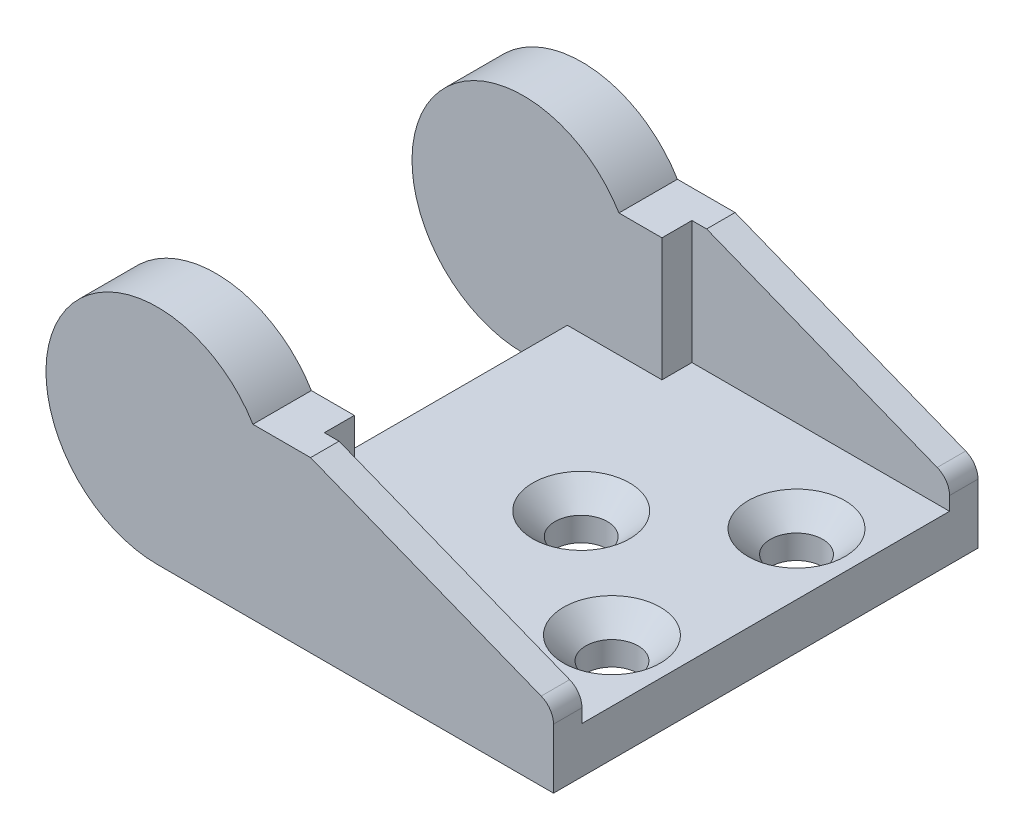
SolidWorks part; units mm, degrees
ref_plane "Front Plane" through (0, 0, 0) normal (0, 0, 1) x (1, 0, 0)
ref_plane "Top Plane" through (0, 0, 0) normal (0, 1, 0) x (1, 0, 0)
ref_plane "Right Plane" through (0, 0, 0) normal (1, 0, 0) x (0, 0, -1)
sketch "Sketch1" plane through (0, 0, 0) normal (0, 0, 1) x (1, 0, 0)
  line L0 (0, -7.25) -> (25.75, -7.25)
  line L1 (25.75, -7.25) -> (25.75, -2.5)
  line L2 (25.75, -2.5) -> (9.9548, 3.75)
  line L3 (9.9548, 3.75) -> (6.2048, 3.75)
  arc A0 (6.2048, 3.75) -> (0, -7.25) centre (0, 0) ccw
  dimension "D1" = 14.5
  dimension "D2" = 33
  dimension "D3" = 11
  dimension "D4" = 3.75
  dimension "D5" = 4.75
extrude "Boss-Extrude1" add sketch "Sketch1" along normal mid plane 27.6
sketch "Sketch2" plane through (0, 0, 0) normal (0, 1, 0) x (1, 0, 0)
  line L0 (25.75, -13.8) -> (25.75, 13.8) construction
  line L1 (25.75, 11.95) -> (9, 11.95)
  line L2 (25.75, 11.95) -> (25.75, -11.95)
  line L3 (25.75, -11.95) -> (9, -11.95)
  line L4 (9, 11.95) -> (9, -11.95)
  line L5 (25.75, 0) -> (0, 0) construction
  dimension "D1" = 23.9
  dimension "D2" = 16.75
extrude "Cut-Extrude1" cut sketch "Sketch2" against normal offset from surface 3 and the other way through all up to face at (12.875, -7.25, 0)
sketch "Sketch3" plane through (0, -7.25, 0) normal (0, -1, 0) x (1, 0, 0)
  line L0 (-7.25, 13.8) -> (-7.25, -13.8) construction
  line L1 (2.85, -10) -> (-7.25, -10)
  line L2 (2.85, -10) -> (2.85, 10)
  line L3 (2.85, 10) -> (-7.25, 10)
  line L4 (-7.25, -10) -> (-7.25, 10)
  line L5 (25.75, 13.8) -> (25.75, -13.8) construction
  line L6 (0, 0) -> (2.85, 0) construction
  dimension "D1" = 22.9
  dimension "D2" = 20
extrude "Cut-Extrude2" cut sketch "Sketch3" against normal through all
sketch "Sketch4" plane through (0, -4.25, 0) normal (0, 1, 0) x (1, 0, 0)
  line L0 (9, -11.95) -> (9, 11.95) construction
  line L1 (2.85, 10) -> (9, 10)
  line L2 (2.85, 10) -> (2.85, -10)
  line L3 (2.85, -10) -> (9, -10)
  line L4 (9, 10) -> (9, -10)
  line L5 (2.85, 10) -> (2.85, -10) construction
  line L6 (2.85, -10) -> (-7.25, -10) construction
extrude "Cut-Extrude3" cut sketch "Sketch4" along normal through all
fillet "Fillet1" radius 1.27 2 edges at (25.75, -2.5, 12.875) (25.75, -2.5, -12.875)
sketch "Sketch5" plane through (0, -4.25, 0) normal (0, 1, 0) x (1, 0, 0)
  line L0 (21.75, 6) -> (21.75, -6) construction
  line L1 (13.75, 0) -> (21.75, 0) construction
  line L2 (25.75, 11.95) -> (25.75, -11.95) construction
  point P0 (21.75, 6)
  point P1 (21.75, -6)
  point P2 (13.75, 0)
  dimension "D1" = 12
  dimension "D2" = 4
  dimension "D3" = 8
hole_wizard "CSK for M3 Flat Head Machine Screw1" positions "3DSketch1" profile "Sketch6" countersink size "M3" standard "ANSI Metric" end condition through all
sketch3d "3DSketch1"
  point P0 (21.75, -4.25, -6)
  point P3 (13.75, -4.25, 0)
  point P6 (21.75, -4.25, 6)
sketch "Sketch6" plane through (21.75, -4.25, -6) normal (1, 0, 0) x (0, 0, 1)
  line L0 (0, 0) -> (0, 3)
  line L1 (0, 3) -> (1.7, 3)
  line L2 (1.7, 3) -> (1.7, 1.45)
  line L3 (1.7, 1.45) -> (3.15, 0)
  line L5 (3.15, 0) -> (0, 0)
  line L6 (-1.7, 1.45) -> (-3.15, 0) construction
  line L11 (0, -6.35) -> (0, 107.95) construction
  dimension "Thru Hole Dia." = 3.4
  dimension "Thru Hole Depth" = 3
  dimension "Near C'Sink Dia." = 6.3
  dimension "Near C'Sink Angle" = 90
